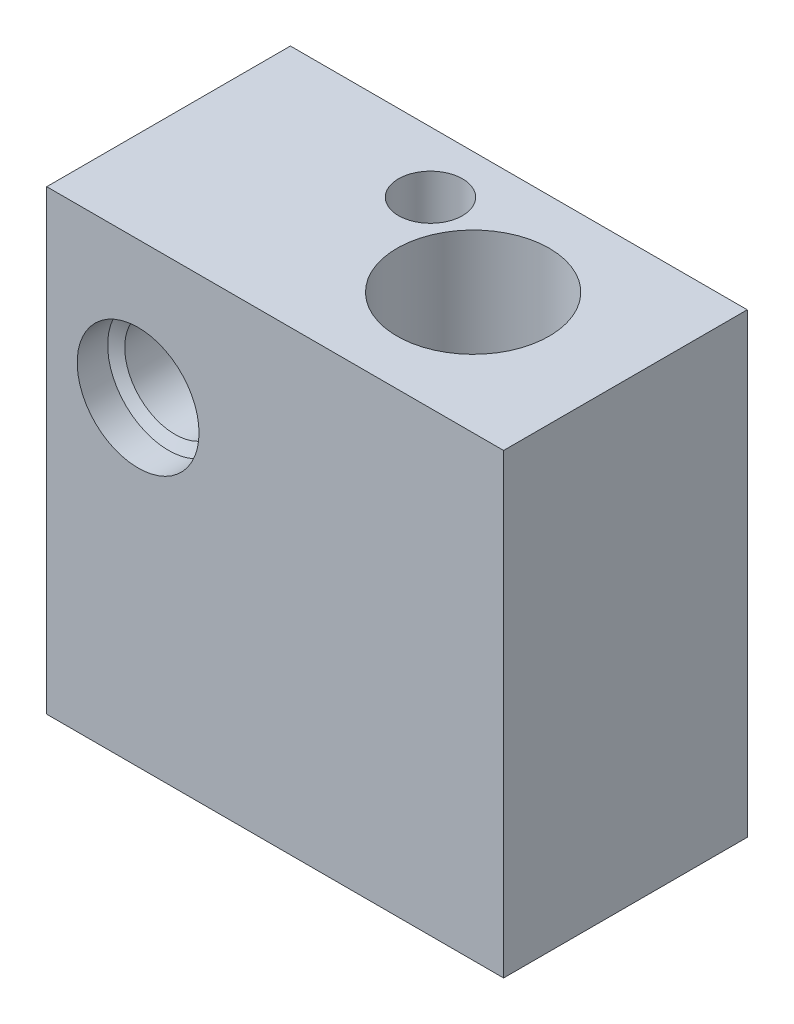
SolidWorks part; units mm, degrees
material "1060 Alloy"
ref_plane "Front Plane" through (0, 0, 0) normal (0, 0, 1) x (1, 0, 0)
ref_plane "Top Plane" through (0, 0, 0) normal (0, 1, 0) x (1, 0, 0)
ref_plane "Right Plane" through (0, 0, 0) normal (1, 0, 0) x (0, 0, -1)
sketch "Sketch1" plane through (0, 0, 0) normal (0, 0, 1) x (1, 0, 0)
  line L1 (-3, 4.5) -> (12, 4.5)
  line L2 (-3, 4.5) -> (-3, -10.5)
  line L3 (-3, -10.5) -> (12, -10.5)
  line L4 (12, 4.5) -> (12, -10.5)
  circle A0 centre (0, 0) radius 1.65
  dimension "D1" = 3.3
  dimension "D2" = 3
  dimension "D3" = 15
  dimension "D4" = 15
  dimension "D5" = 4.5
extrude "Boss-Extrude1" add sketch "Sketch1" along normal blind 8
cosmetic thread "Cosmetic Thread1" parameters "D2"=4
sketch "Sketch2" plane through (0, -10.5, 0) normal (0, -1, 0) x (1, 0, 0)
  line L0 (7, 4) -> (12, 4) construction
  line L1 (12, 8) -> (12, 0) construction
  circle A0 centre (7, 4) radius 2.5
  dimension "D1" = 5
  dimension "D2" = 7
extrude "Cut-Extrude1" cut sketch "Sketch2" against normal through all
sketch "Sketch3" plane through (0, -10.5, 0) normal (0, -1, 0) x (1, 0, 0)
  line L0 (-3, 0) -> (12, 0) construction
  line L1 (-3, 8) -> (-3, 0) construction
  circle A0 centre (3.6, 2) radius 1.05
  dimension "D1" = 2.1
  dimension "D3" = 6.6
  dimension "D2" = 2
extrude "Cut-Extrude2" cut sketch "Sketch3" against normal through all
hole_wizard "Ø4.0 (4) Diameter Hole1" positions "Sketch6" profile "Sketch5" hole size "Ø4.0" standard "ANSI Metric"
sketch "Sketch6" plane through (0, 0, 8) normal (0, 0, 1) x (1, 0, 0)
  point P0 (0, 0)
sketch "Sketch5" plane through (0, 0, 8) normal (1, 0, 0) x (0, -1, 0)
  line L0 (0, 0) -> (0, 2.2017)
  line L1 (0, 2.2017) -> (2, 1)
  line L2 (2, 1) -> (2, 0)
  line L5 (2, 0) -> (0, 0)
  line L10 (0, 2.2017) -> (-2, 1) construction
  line L11 (0, -6.35) -> (0, 107.95) construction
  dimension "Hole Dia." = 4
  dimension "Hole Depth" = 1
  dimension "Drill Angle" = 118
